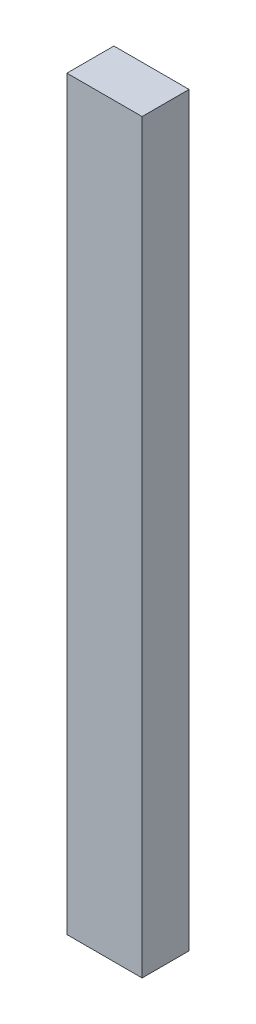
SolidWorks part; units mm, degrees
ref_plane "Alzado" through (0, 0, 0) normal (0, 0, 1) x (1, 0, 0)
ref_plane "Planta" through (0, 0, 0) normal (0, 1, 0) x (1, 0, 0)
ref_plane "Vista lateral" through (0, 0, 0) normal (1, 0, 0) x (0, 0, -1)
sketch "Croquis1" plane through (0, 0, 0) normal (0, 0, 1) x (1, 0, 0)
  line L1 (0, 0) -> (-25.4, 0)
  line L2 (0, 0) -> (0, 252)
  line L3 (0, 252) -> (-25.4, 252)
  line L4 (-25.4, 0) -> (-25.4, 252)
  dimension "D1" = 252
  dimension "D2" = 25.4
extrude "Saliente-Extruir1" add sketch "Croquis1" along normal blind 15.875
sketch "Croquis2" plane through (0, 0, 0) normal (0, 0, -1) x (-1, 0, 0)
  line L0 (0, 244) -> (25.4, 244) construction
  line L1 (0, 0) -> (0, 252) construction
  line L2 (25.4, 252) -> (25.4, 0) construction
  line L3 (0, 252) -> (25.4, 252) construction
  line L4 (0, 243) -> (0, 245)
  line L5 (0, 245) -> (9.2188, 247)
  line L6 (9.2188, 247) -> (9.2188, 249.5)
  line L7 (9.2188, 249.5) -> (0, 252)
  line L8 (0, 243) -> (9.2188, 241)
  line L9 (9.2188, 241) -> (9.2188, 238.5)
  dimension "D1" = 8
  dimension "D2" = 1
  dimension "D3" = 3
  dimension "D4" = 2.5
  dimension "D5" = 2.5
